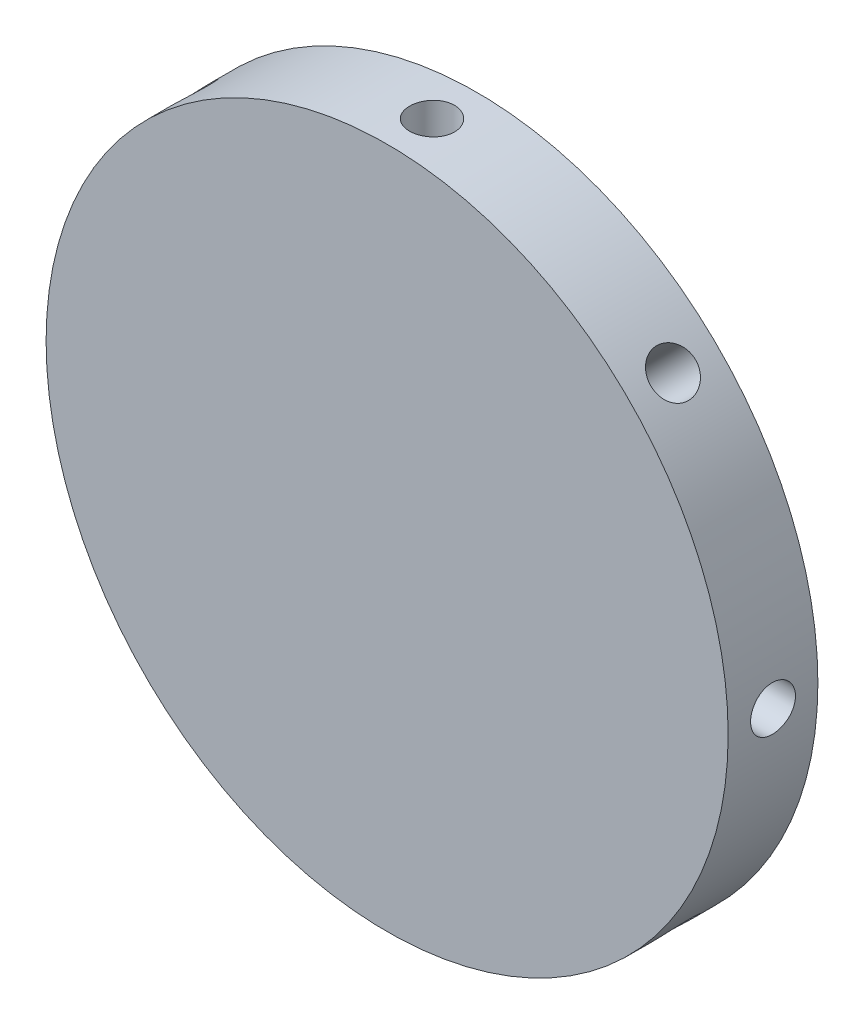
SolidWorks part; units mm, degrees
ref_plane "Front Plane" through (0, 0, 0) normal (0, 0, 1) x (1, 0, 0)
ref_plane "Top Plane" through (0, 0, 0) normal (0, 1, 0) x (1, 0, 0)
ref_plane "Right Plane" through (0, 0, 0) normal (1, 0, 0) x (0, 0, -1)
sketch "Sketch1" plane through (0, 0, 0) normal (0, 0, 1) x (1, 0, 0)
  circle A0 centre (0, 0) radius 38
  dimension "D1" = 76
extrude "Boss-Extrude1" add sketch "Sketch1" along normal blind 10
ref_plane "Attachments" through (0, 38, 0) normal (0, 1, 0) x (1, 0, 0)
sketch "Sketch2" plane through (0, 38, 0) normal (0, 1, 0) x (1, 0, 0)
  line L0 (0, 0) -> (0, -5) construction
  circle A1 centre (0, -5) radius 2.5
  dimension "D2" = 5
  dimension "D1" = 5
extrude "Cut-Extrude1" cut sketch "Sketch2" against normal blind 10
pattern_circular "CirPattern1" count 8 over 360 about axis through (0, 0, 0) along (0, 0, 1) of "Cut-Extrude1"
